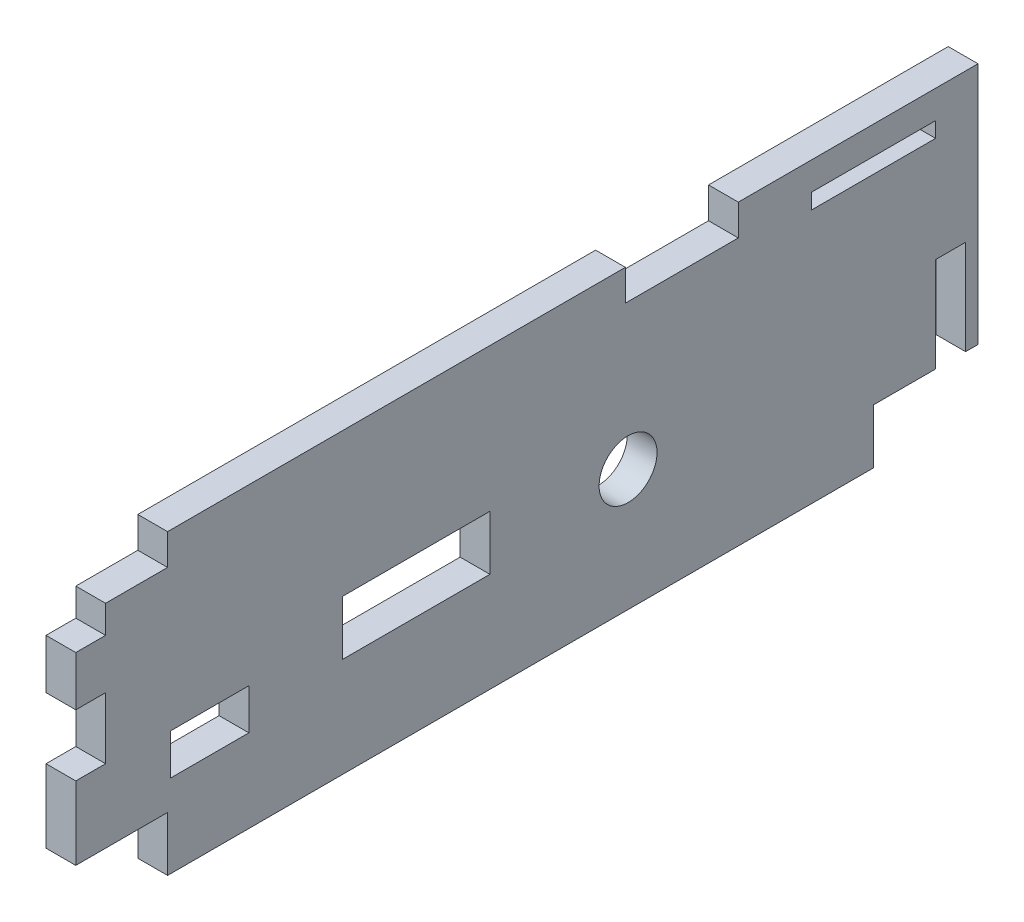
SolidWorks part; units mm, degrees
ref_plane "Front" through (0, 0, 0) normal (0, 0, 1) x (1, 0, 0)
ref_plane "Top" through (0, 0, 0) normal (0, 1, 0) x (1, 0, 0)
ref_plane "Right" through (0, 0, 0) normal (1, 0, 0) x (0, 0, -1)
sketch "Sketch2" plane through (0, 0, 0) normal (1, 0, 0) x (0, 0, -1)
  line L0 (0, 4.7244) -> (84.963, 4.7244) construction
  line L1 (0, 24.0284) -> (84.963, 24.0284)
  line L2 (0, 24.0284) -> (0, 0)
  line L3 (0, 0) -> (84.963, 0)
  line L4 (84.963, 24.0284) -> (84.963, 0)
  line L5 (6.6294, 9.3853) -> (14.6685, 9.3853)
  line L6 (6.6294, 9.3853) -> (6.6294, 5.207)
  line L7 (6.6294, 5.207) -> (14.6685, 5.207)
  line L8 (14.6685, 9.3853) -> (14.6685, 5.207)
  line L9 (24.257, 6.9215) -> (39.3446, 6.9215)
  line L10 (24.257, 6.9215) -> (24.257, 12.5095)
  line L11 (24.257, 12.5095) -> (39.3446, 12.5095)
  line L12 (39.3446, 6.9215) -> (39.3446, 12.5095)
  line L13 (53.486, 12.1412) -> (53.486, 4.7244) construction
  line L14 (6.35, 24.0284) -> (6.35, 27.2034)
  line L15 (6.35, 27.2034) -> (53.213, 27.2034)
  line L16 (84.963, 24.0284) -> (86.7664, 24.0284)
  line L17 (6.35, 4.7244) -> (6.35, 1.5494)
  line L18 (6.35, 1.5494) -> (46.863, 1.5494)
  line L19 (46.863, 1.5494) -> (46.863, 4.7244)
  line L20 (46.863, 4.7244) -> (84.963, 4.7244)
  line L21 (6.35, 4.7244) -> (0, 4.7244)
  line L22 (86.7664, 24.0284) -> (86.7664, 4.7244)
  line L23 (86.7664, 24.0284) -> (89.3064, 24.0284)
  line L24 (89.3064, 24.0284) -> (89.3064, 4.7244)
  line L25 (84.963, 12.0142) -> (86.7664, 12.0142)
  line L26 (86.7664, 4.7244) -> (89.3064, 4.7244)
  line L27 (84.963, 22.7584) -> (72.263, 22.7584)
  line L28 (42.4815, 24.0284) -> (42.4815, 0) construction
  line L29 (-3.048, 4.7244) -> (0, 4.7244)
  line L30 (-3.048, 9.8044) -> (-3.048, 4.7244)
  line L31 (-3.048, 9.8044) -> (0, 9.8044)
  line L32 (-3.048, 16.1036) -> (0, 16.1036)
  line L33 (-3.048, 21.1836) -> (-3.048, 16.1036)
  line L34 (0, 21.1836) -> (-3.048, 21.1836)
  line L35 (53.213, 27.2034) -> (53.213, 24.0284)
  line L36 (72.263, 22.7584) -> (72.263, 24.5618)
  line L37 (72.263, 24.5618) -> (84.963, 24.5618)
  line L38 (84.963, 24.5618) -> (84.963, 24.0284)
  line L39 (89.3064, 24.0284) -> (89.3064, 27.2034)
  line L40 (89.3064, 27.2034) -> (64.77, 27.2034)
  line L41 (64.77, 27.2034) -> (64.77, 24.0284)
  circle A0 centre (53.486, 9.1758) radius 2.9655
  dimension "D11" = 5.9309
  dimension "D13" = 11.176
  dimension "D1" = 84.963
  dimension "D2" = 8.0391
  dimension "D3" = 15.0876
  dimension "D4" = 4.6609
  dimension "D5" = 4.1783
  dimension "D6" = 6.6294
  dimension "D7" = 7.7851
  dimension "D8" = 5.588
  dimension "D9" = 9.5885
  dimension "D10" = 4.7244
  dimension "D12" = 7.4168
  dimension "D14" = 19.304
  dimension "D15" = 6.35
  dimension "D16" = 3.175
  dimension "D17" = 3.175
  dimension "D18" = 38.1
  dimension "D19" = 3.048
  dimension "D20" = 2.8448
  dimension "D21" = 5.08
  dimension "D22" = 5.08
  dimension "D23" = 31.75
  dimension "D24" = 1.8034
  dimension "D25" = 1.27
  dimension "D26" = 12.7
extrude "Boss-Extrude1" add sketch "Sketch2" along normal blind 3.048
sketch "Sketch3" plane through (0, 0, 0) normal (-1, 0, 0) x (0, 0, 1)
  line L0 (-72.263, 22.7584) -> (-72.263, 24.5618) construction
  line L1 (-84.963, 24.5618) -> (-72.263, 24.5618)
  line L2 (-84.963, 24.5618) -> (-84.963, 24.3332)
  line L3 (-84.963, 24.3332) -> (-72.263, 24.3332)
  line L4 (-72.263, 24.5618) -> (-72.263, 24.3332)
  line L5 (-84.963, 22.7584) -> (-72.263, 22.7584) construction
  dimension "D1" = 1.5748
extrude "made hood slot smaller" add sketch "Sketch3" against normal up to vertex (3.048 mm away)
sketch "Sketch4" plane through (3.048, 0, 0) normal (1, 0, 0) x (0, 0, -1)
  line B0 (6.6294, 5.207) -> (14.6685, 5.207)
  line B1 (24.257, 6.9215) -> (39.3446, 6.9215)
  line B2 (14.6685, 9.3853) -> (14.6685, 5.207)
  line B3 (6.6294, 9.3853) -> (14.6685, 9.3853)
  line B4 (6.6294, 9.3853) -> (6.6294, 5.207)
  line B5 (24.257, 6.9215) -> (24.257, 12.5095)
  line B6 (24.257, 12.5095) -> (39.3446, 12.5095)
  line B7 (39.3446, 6.9215) -> (39.3446, 12.5095)
  line B8 (46.863, 4.7244) -> (84.963, 4.7244)
  line B9 (0, 16.1036) -> (0, 9.8044)
  circle B10 centre (53.486, 9.1758) radius 2.9655
sketch_block_instance "Block1-1"
sketch_block "Block1"
sketch "Sketch5" plane through (3.048, 0, 0) normal (1, 0, 0) x (0, 0, -1)
  line L0 (86.7664, 4.7244) -> (89.3064, 4.7244) construction
  line L1 (84.963, 12.0142) -> (88.0364, 12.0142)
  line L2 (84.963, 12.0142) -> (84.963, 4.7244)
  line L3 (84.963, 4.7244) -> (88.0364, 4.7244)
  line L4 (88.0364, 12.0142) -> (88.0364, 4.7244)
extrude "Cut-Extrude1" cut sketch "Sketch5" against normal through all
sketch "Sketch7" plane through (3.048, 0, 0) normal (1, 0, 0) x (0, 0, -1)
  line L0 (-3.048, 4.7244) -> (-3.048, 2.3114)
  line L1 (6.35, 4.7244) -> (-3.048, 4.7244) construction
  line L2 (-3.048, 2.3114) -> (6.35, 2.3114)
  line L3 (6.35, 4.7244) -> (6.35, 1.5494) construction
  line L4 (6.35, 2.3114) -> (6.35, -3.2766)
  line L5 (6.35, -3.2766) -> (78.613, -3.2766)
  line L6 (78.613, -3.2766) -> (78.613, 2.3114)
  line L7 (78.613, 2.3114) -> (84.963, 2.3114)
  line L8 (84.963, 2.3114) -> (84.963, 4.7244)
  line L9 (-3.048, 4.7244) -> (84.963, 4.7244)
  line L10 (88.0364, 4.7244) -> (88.0364, 2.3114)
  line L11 (88.0364, 2.3114) -> (89.3064, 2.3114)
  line L12 (89.3064, 2.3114) -> (89.3064, 4.7244)
  line L13 (88.0364, 4.7244) -> (89.3064, 4.7244)
  dimension "D1" = 2.413
  dimension "D2" = 5.588
  dimension "D3" = 6.35
extrude "Boss-Extrude2" add sketch "Sketch7" against normal blind 3.048
